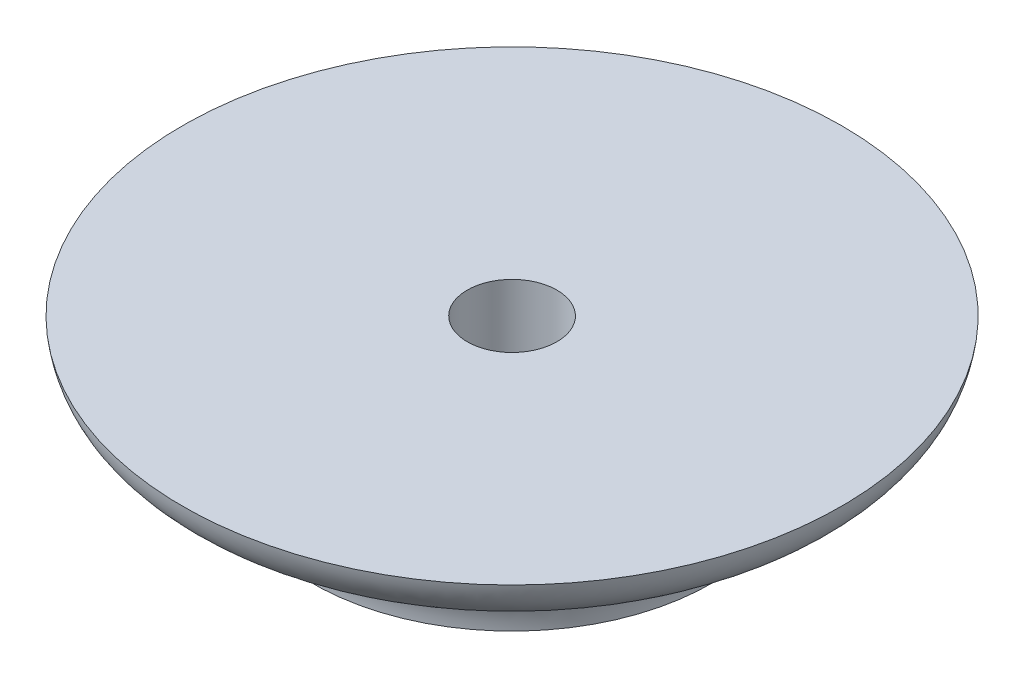
SolidWorks part; units mm, degrees
material "6061 Alloy"
ref_plane "Front Plane" through (0, 0, 0) normal (0, 0, 1) x (1, 0, 0)
ref_plane "Top Plane" through (0, 0, 0) normal (0, 1, 0) x (1, 0, 0)
ref_plane "Right Plane" through (0, 0, 0) normal (1, 0, 0) x (0, 0, -1)
sketch "Sketch1" plane through (0, 0, 0) normal (0, 1, 0) x (1, 0, 0)
  circle A0 centre (0, 0) radius 12.7
  dimension "D1" = 25.4
extrude "Boss-Extrude1" add sketch "Sketch1" along normal blind 5.08
sketch "Sketch2" plane through (0, 0, 0) normal (1, 0, 0) x (0, 0, -1)
  line L0 (-12.7, 5.08) -> (12.7, 5.08)
  line L1 (12.7, 5.08) -> (12.7, 0)
  line L2 (12.7, 0) -> (-12.7, 0)
  line L3 (-12.7, 0) -> (-12.7, 5.08)
  line L4 (0, 0) -> (0, 31.9805) construction
  spline S0 degree 3 poles (-12.7, 5.08) (-12.2925, 2.0708) (-7.6941, 3.6367) (-7.6941, 0) knots 0 0 0 0 1 1 1 1
revolve "Cut-Revolve1" cut sketch "Sketch2" angle 360 about L4
sketch "Sketch4" plane through (0, 0, 0) normal (0, -1, 0) x (-1, 0, 0)
  point P0 (0, 0)
hole_wizard "#8-32 Tapped Hole1" positions "Sketch4" profile "Sketch5" tap size "#8-32" standard "ANSI Inch" end condition through all
cosmetic thread "Hole Thread1" parameters "D2"=4.1656
sketch "Sketch5" plane through (0, 0, 0) normal (1, 0, 0) x (0, 0, -1)
  line L0 (0, 0) -> (0, 5.08)
  line L1 (0, 5.08) -> (1.7272, 5.08)
  line L2 (1.7272, 5.08) -> (1.7272, 0)
  line L5 (1.7272, 0) -> (0, 0)
  line L11 (0, -6.35) -> (0, 107.95) construction
  dimension "Thru Tap Drill Dia." = 3.4544
  dimension "Thru Tap Drill Depth" = 5.08
sketch "Sketch6" plane through (0, 5.08, 0) normal (0, 1, 0) x (1, 0, 0)
  line L0 (0, 12.7) -> (0, 4.2117) construction
  line L1 (-2.54, 6.7437) -> (2.54, 6.7437)
  line L2 (-2.54, 6.7437) -> (-2.54, -6.7437)
  line L3 (-2.54, -6.7437) -> (2.54, -6.7437)
  line L4 (2.54, 6.7437) -> (2.54, -6.7437)
  circle A0 centre (0, 0) radius 12.7 construction
  point P9 (0, 6.7437)
  dimension "D1" = 5.08
  dimension "D2" = 13.4874
  dimension "D3" = 6.7437
